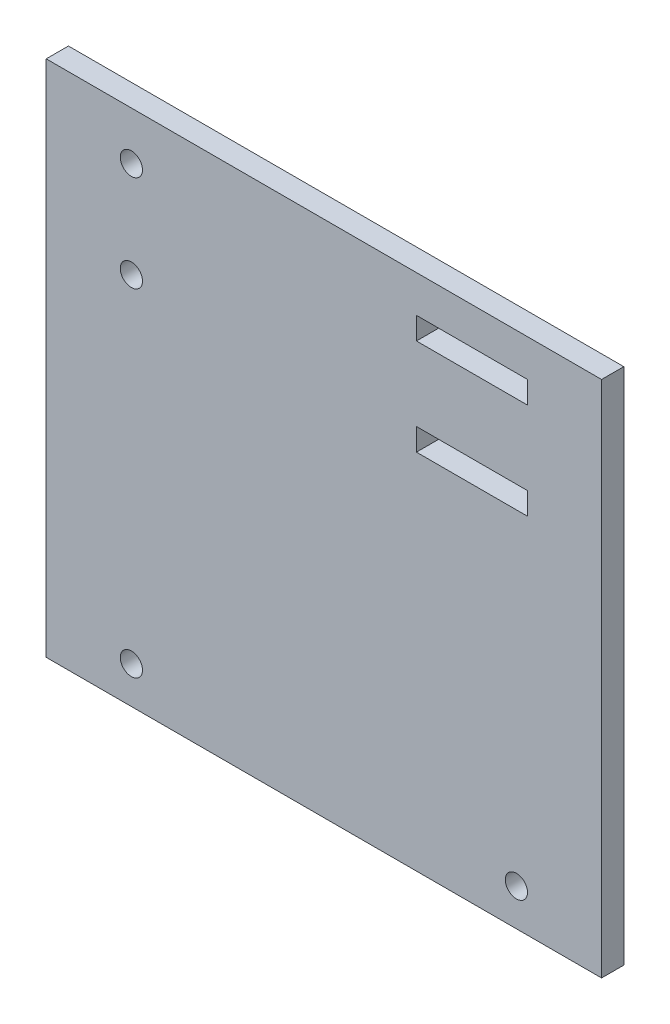
SolidWorks part; units mm, degrees
ref_plane "Front Plane" through (0, 0, 0) normal (0, 0, 1) x (1, 0, 0)
ref_plane "Top Plane" through (0, 0, 0) normal (0, 1, 0) x (1, 0, 0)
ref_plane "Right Plane" through (0, 0, 0) normal (1, 0, 0) x (0, 0, -1)
sketch "Esquisse1" plane through (0, 0, 0) normal (0, 0, 1) x (1, 0, 0)
  line L0 (-0.1837, 14.1633) -> (14.8163, 14.1633)
  line L1 (-50.1837, 32.1633) -> (24.8163, 32.1633)
  line L2 (-50.1837, 32.1633) -> (-50.1837, -37.8367)
  line L3 (-50.1837, -37.8367) -> (24.8163, -37.8367)
  line L4 (24.8163, 32.1633) -> (24.8163, -37.8367)
  line L5 (-0.1837, 14.1633) -> (-0.1837, 11.1633)
  line L6 (-0.1837, 11.1633) -> (14.8163, 11.1633)
  line L7 (14.8163, 14.1633) -> (14.8163, 11.1633)
  line L9 (-0.1837, 27.1633) -> (14.8163, 27.1633)
  line L10 (-0.1837, 27.1633) -> (-0.1837, 24.1633)
  line L11 (-0.1837, 24.1633) -> (14.8163, 24.1633)
  line L12 (14.8163, 27.1633) -> (14.8163, 24.1633)
  circle A0 centre (-38.6837, 25.6633) radius 1.5
  circle A1 centre (-38.6837, 12.6633) radius 1.5
  circle A3 centre (-38.6837, -32.8367) radius 1.5
  circle A4 centre (13.3163, -32.8367) radius 1.5
  point P21 (-38.6837, -32.8367)
  point P22 (13.3163, -32.8367)
  dimension "D3" = 11.5
  dimension "D6" = 1.5
  dimension "D7" = 10
  dimension "D10" = 5
  dimension "D11" = 1.5
  dimension "D1" = 75
  dimension "D2" = 70
  dimension "D4" = 3
  dimension "D5" = 5
  dimension "D8" = 11.5
  dimension "D9" = 10
extrude "Boss.-Extru.1" add sketch "Esquisse1" along normal blind 3
